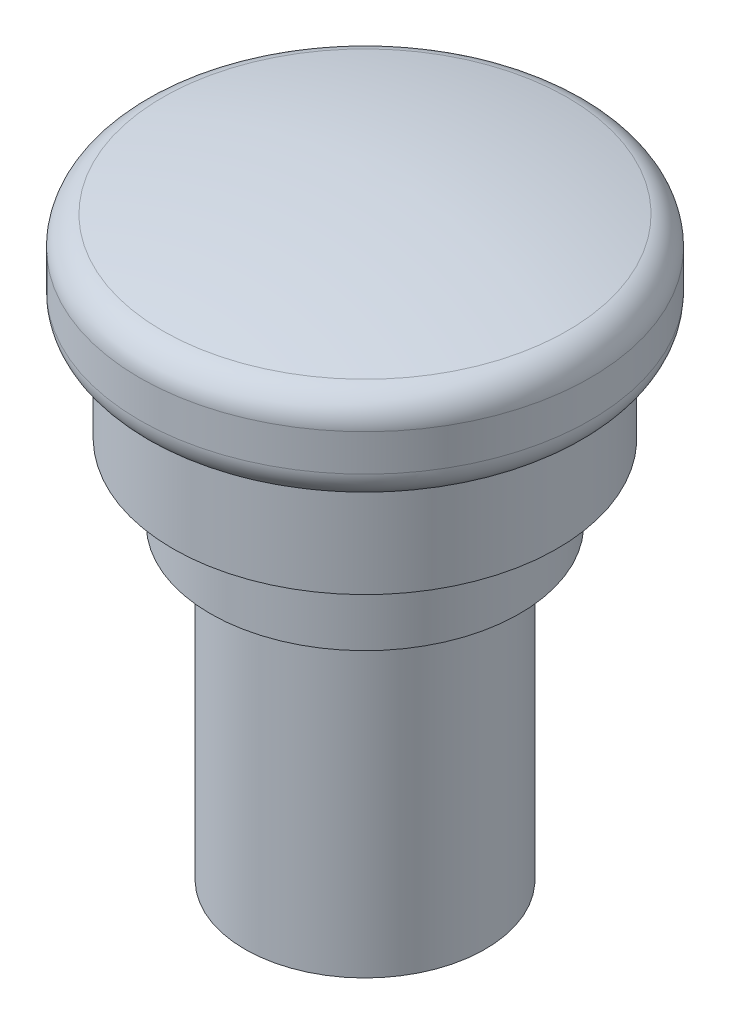
SolidWorks part; units mm, degrees
material "ABS"
ref_plane "Front Plane" through (0, 0, 0) normal (0, 0, 1) x (1, 0, 0)
ref_plane "Top Plane" through (0, 0, 0) normal (0, 1, 0) x (1, 0, 0)
ref_plane "Right Plane" through (0, 0, 0) normal (1, 0, 0) x (0, 0, -1)
sketch "Sketch1" plane through (0, 0, 0) normal (0, 1, 0) x (1, 0, 0)
  circle A0 centre (0, 0) radius 8
  dimension "D1" = 16
extrude "Boss-Extrude1" add sketch "Sketch1" along normal blind 20.5
sketch "Sketch2" plane through (0, 20.5, 0) normal (0, 1, 0) x (1, 0, 0)
  circle A0 centre (0, 0) radius 10.3
  dimension "D1" = 20.6
extrude "Boss-Extrude2" add sketch "Sketch2" along normal blind 4
sketch "Sketch3" plane through (0, 24.5, 0) normal (0, 1, 0) x (1, 0, 0)
  circle A0 centre (0, 0) radius 10.9
  dimension "D1" = 21.8
extrude "Boss-Extrude3" add sketch "Sketch3" along normal blind 1
sketch "Sketch4" plane through (0, 25.5, 0) normal (0, 1, 0) x (1, 0, 0)
  circle A0 centre (0, 0) radius 12.8
  dimension "D1" = 25.6
extrude "Boss-Extrude4" add sketch "Sketch4" along normal blind 6.5
sketch "Sketch5" plane through (0, 0, 0) normal (1, 0, 0) x (0, 0, -1)
  line L0 (0, 32) -> (0, 40)
  line L1 (12.8, 32) -> (-12.8, 32) construction
  line L2 (-10.9, 25.5) -> (10.9, 25.5) construction
  line L3 (0, 35) -> (-15, 35) construction
  line L4 (-15, 38) -> (-15, 32)
  line L5 (-12.8, 32) -> (-15, 32)
  line L6 (-12.8, 32) -> (0, 32)
  arc A0 (0, 40) -> (-15, 38) centre (0, -17.25) ccw
  point P11 (-15, 35)
  dimension "D1" = 14.5
  dimension "D2" = 15
  dimension "D4" = 6
revolve "Revolve1" add sketch "Sketch5" angle 360 about L0
fillet "Fillet1" radius 2 2 edges at (0, 32, -15) (0, 38, -15)
